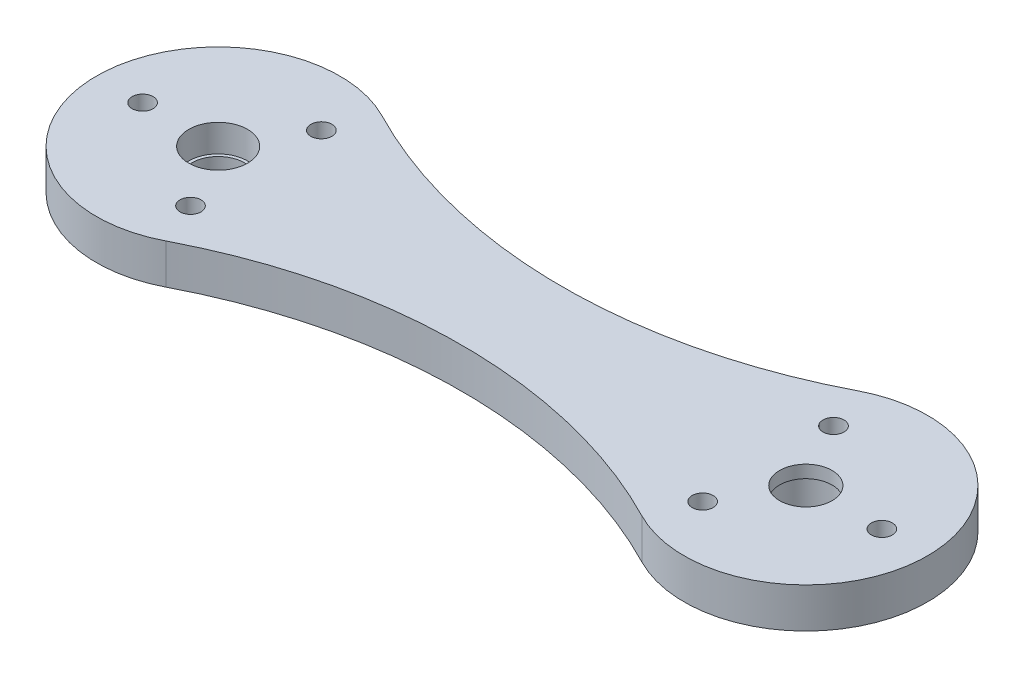
SolidWorks part; units mm, degrees
material "Stainless Steel (ferritic)"
ref_plane "Front Plane" through (0, 0, 0) normal (0, 0, 1) x (1, 0, 0)
ref_plane "Top Plane" through (0, 0, 0) normal (0, 1, 0) x (1, 0, 0)
ref_plane "Right Plane" through (0, 0, 0) normal (1, 0, 0) x (0, 0, -1)
sketch "Sketch1" plane through (0, 0, 0) normal (0, 1, 0) x (1, 0, 0)
  line L0 (-35, 0) -> (35, 0) construction
  line L1 (-11.7822, 6) -> (8.9487, 6) construction
  arc A0 (-28.3494, 12.8849) -> (-28.3494, -12.8849) centre (-35, 0) ccw
  arc A1 (28.3494, -12.8849) -> (28.3494, 12.8849) centre (35, 0) ccw
  arc A2 (-28.3494, 12.8849) -> (28.3494, 12.8849) centre (0, 67.8088) ccw
  arc A3 (-28.3494, -12.8849) -> (28.3494, -12.8849) centre (0, -67.8088) cw
  dimension "D2" = 29
  dimension "D1" = 70
  dimension "D3" = 6
extrude "Boss-Extrude1" add sketch "Sketch1" along normal blind 4.7625
sketch "Sketch2" plane through (0, 4.7625, 0) normal (0, 1, 0) x (1, 0, 0)
  circle A0 centre (-35, 0) radius 3.5
  dimension "D1" = 7
extrude "Cut-Extrude1" cut sketch "Sketch2" against normal offset from surface (3.2625 mm away) 1.5 up to face at (0, 0, 0)
sketch "Sketch3" plane through (0, 1.5, 0) normal (0, 1, 0) x (1, 0, 0)
  circle A0 centre (-35, 0) radius 3.125
  dimension "D1" = 6.25
extrude "Cut-Extrude2" cut sketch "Sketch3" against normal through all
sketch "Sketch4" plane through (0, 4.7625, 0) normal (0, 1, 0) x (1, 0, 0)
  circle A0 centre (35, 0) radius 3
  dimension "D1" = 6
extrude "Cut-Extrude3" [suppressed] cut sketch "Sketch4" against normal through all
sketch "Sketch5" [suppressed] plane through (0, 4.7625, 0) normal (0, 1, 0) x (1, 0, 0)
  circle A0 centre (35, 0) radius 5
  circle A1 centre (35, 0) radius 3 construction
  dimension "D1" = 2
extrude "Cut-Extrude4" [suppressed] cut sketch "Sketch5" against normal blind 2
sketch "Sketch6" plane through (0, 0, 0) normal (0, -1, 0) x (1, 0, 0)
  circle A0 centre (35, 0) radius 3.125
  circle A1 centre (-35, 0) radius 3.125 construction
extrude "Cut-Extrude5" cut sketch "Sketch6" against normal through all
sketch "Sketch7" plane through (0, 0, 0) normal (0, -1, 0) x (1, 0, 0)
  circle A0 centre (35, 0) radius 3.5
  circle A1 centre (-35, 0) radius 3.5 construction
extrude "Cut-Extrude6" cut sketch "Sketch7" against normal offset from surface (3.2625 mm away) 1.5 up to face at (35, 4.7625, -3.125)
hole_wizard "M3x0.5 Tapped Hole1" positions "Sketch9" profile "Sketch8" tap size "M3x0.5" standard "Ansi Metric" end condition through all
sketch "Sketch9" plane through (0, 4.7625, 0) normal (0, 1, 0) x (-1, 0, 0)
  line L0 (44, 0) -> (35, 0) construction
  line L1 (35, 0) -> (30.5, 7.7942) construction
  line L3 (35, 0) -> (30.5, -7.7942) construction
  circle A0 centre (35, 0) radius 9 construction
  point P0 (30.5, 7.7942)
  point P1 (44, 0)
  point P3 (30.5, -7.7942)
  dimension "D1" = 18
  dimension "D2" = 120
  dimension "D3" = 120
sketch "Sketch8" plane through (-30.5, 4.7625, 7.7942) normal (1, 0, 0) x (0, 0, 1)
  line L0 (0, 0) -> (0, 4.7625)
  line L1 (0, 4.7625) -> (1.25, 4.7625)
  line L2 (1.25, 4.7625) -> (1.25, 0)
  line L5 (1.25, 0) -> (0, 0)
  line L11 (0, -6.35) -> (0, 107.95) construction
  dimension "Thru Tap Drill Dia." = 2.5
  dimension "Thru Tap Drill Depth" = 4.7625
cosmetic thread "Hole Thread1" parameters "D2"=3
cosmetic thread "Hole Thread2" parameters "D2"=3
cosmetic thread "Hole Thread3" parameters "D2"=3
hole_wizard "M3x0.5 Tapped Hole2" positions "Sketch11" profile "Sketch10" tap size "M3x0.5" standard "Ansi Metric" end condition through all
sketch "Sketch11" plane through (0, 0, 0) normal (0, -1, 0) x (1, 0, 0)
  line L0 (44, 0) -> (35, 0) construction
  line L1 (35, 0) -> (30.5, 7.7942) construction
  line L4 (35, 0) -> (30.5, -7.7942) construction
  circle A0 centre (35, 0) radius 9 construction
  point P0 (43.9998, -0.0521)
  point P1 (30.5, 7.7942)
  point P3 (30.5, -7.7942)
  dimension "D1" = 18
  dimension "D2" = 120
  dimension "D3" = 120
sketch "Sketch10" plane through (43.9998, 0, -0.0521) normal (1, 0, 0) x (0, 0, -1)
  line L0 (0, 0) -> (0, 4.7625)
  line L1 (0, 4.7625) -> (1.25, 4.7625)
  line L2 (1.25, 4.7625) -> (1.25, 0)
  line L5 (1.25, 0) -> (0, 0)
  line L11 (0, -6.35) -> (0, 107.95) construction
  dimension "Thru Tap Drill Dia." = 2.5
  dimension "Thru Tap Drill Depth" = 4.7625
cosmetic thread "Hole Thread4" parameters "D2"=3
cosmetic thread "Hole Thread5" parameters "D2"=3
cosmetic thread "Hole Thread6" parameters "D2"=3
